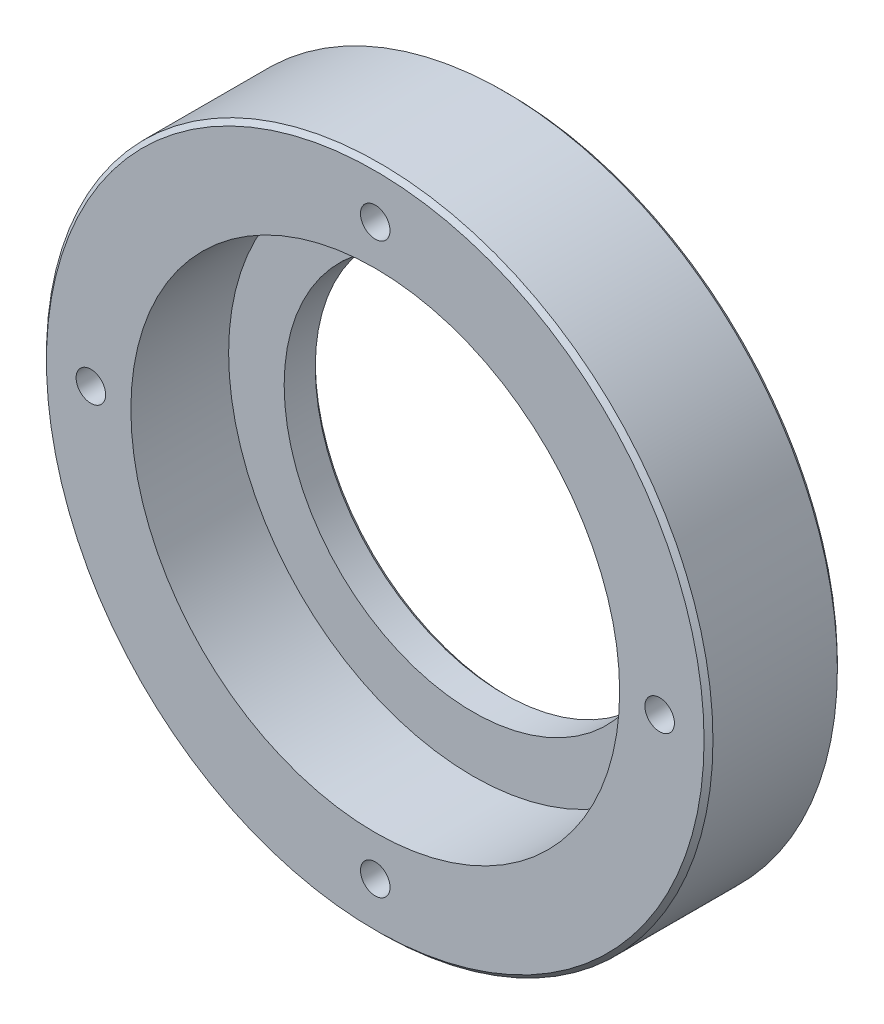
SolidWorks part; units mm, degrees
ref_plane "Front Plane" through (0, 0, 0) normal (0, 0, 1) x (1, 0, 0)
ref_plane "Top Plane" through (0, 0, 0) normal (0, 1, 0) x (1, 0, 0)
ref_plane "Right Plane" through (0, 0, 0) normal (1, 0, 0) x (0, 0, -1)
sketch "Sketch1" plane through (0, 0, 0) normal (0, 1, 0) x (1, 0, 0)
  line L0 (75, 0) -> (0, 0)
  line L1 (0, 0) -> (0, -30)
  line L2 (0, -30) -> (75, -30)
  line L3 (75, -30) -> (75, 0)
  line L4 (0, 0) -> (0, -30) construction
revolve "Revolve1" add sketch "Sketch1" angle 360 about L4
hole_wizard "CBORE for M80 Hex Head Bolt1" positions "Sketch3" profile "Sketch2" counterbore size "M80" standard "ANSI Metric"
sketch "Sketch3" plane through (0, 0, 30) normal (0, 0, 1) x (1, 0, 0)
  point P0 (0, 0)
sketch "Sketch2" plane through (0, 0, 30) normal (1, 0, 0) x (0, -1, 0)
  line L0 (0, 0) -> (0, 30)
  line L1 (0, 30) -> (42.5, 30)
  line L3 (42.5, 30) -> (42.5, 22)
  line L4 (42.5, 22) -> (55, 22)
  line L5 (55, 22) -> (55, 0)
  line L7 (55, 0) -> (0, 0)
  line L11 (0, -6.35) -> (0, 107.95) construction
  dimension "Thru Hole Dia." = 85
  dimension "Thru Hole Depth" = 30
  dimension "C'Bore Dia." = 110
  dimension "C'Bore Depth" = 22
hole_wizard "Hole1" positions "Sketch5" profile "Sketch4" legacy
sketch "Sketch5" plane through (0, 0, 0) normal (0, 0, -1) x (-1, 0, 0)
  point P0 (45.2548, 45.2548)
  point P1 (-45.2548, 45.2548)
  point P2 (-45.2548, -45.2548)
  point P3 (45.2548, -45.2548)
sketch "Sketch4" plane through (-45.2548, 45.2548, 0) normal (1, 0, 0) x (0, 1, 0)
  line L0 (0, 0) -> (0, 22.5164)
  line L1 (0, 22.5164) -> (4.188, 20)
  line L2 (4.188, 20) -> (4.188, 0)
  line L4 (4.188, 0) -> (0, 0)
  line L6 (0, 22.5164) -> (-4.188, 20) construction
  line L7 (0, -4.2442) -> (0, 117.3081) construction
  dimension "Diameter" = 8.376
  dimension "Depth" = 20
  dimension "Drill Angle" = 118
hole_wizard "M6 Clearance Hole1" positions "Sketch7" profile "Sketch6" hole size "M6" standard "ANSI Metric"
sketch "Sketch7" plane through (0, 0, 30) normal (0, 0, 1) x (1, 0, 0)
  point P0 (0, 64)
  point P1 (0, -64)
  point P2 (64, 0)
  point P3 (-64, 0)
sketch "Sketch6" plane through (0, 64, 30) normal (1, 0, 0) x (0, -1, 0)
  line L0 (0, 0) -> (0, 13.997)
  line L1 (0, 13.997) -> (3.3235, 12)
  line L2 (3.3235, 12) -> (3.3235, 0)
  line L5 (3.3235, 0) -> (0, 0)
  line L10 (0, 13.997) -> (-3.3235, 12) construction
  line L11 (0, -6.35) -> (0, 107.95) construction
  dimension "Hole Dia." = 6.647
  dimension "Hole Depth" = 12
  dimension "Drill Angle" = 118
chamfer "Chamfer1" distance 1 angle 45 3 edges at (42.5, 0, 0) (75, 0, 0) (75, 0, 30)
